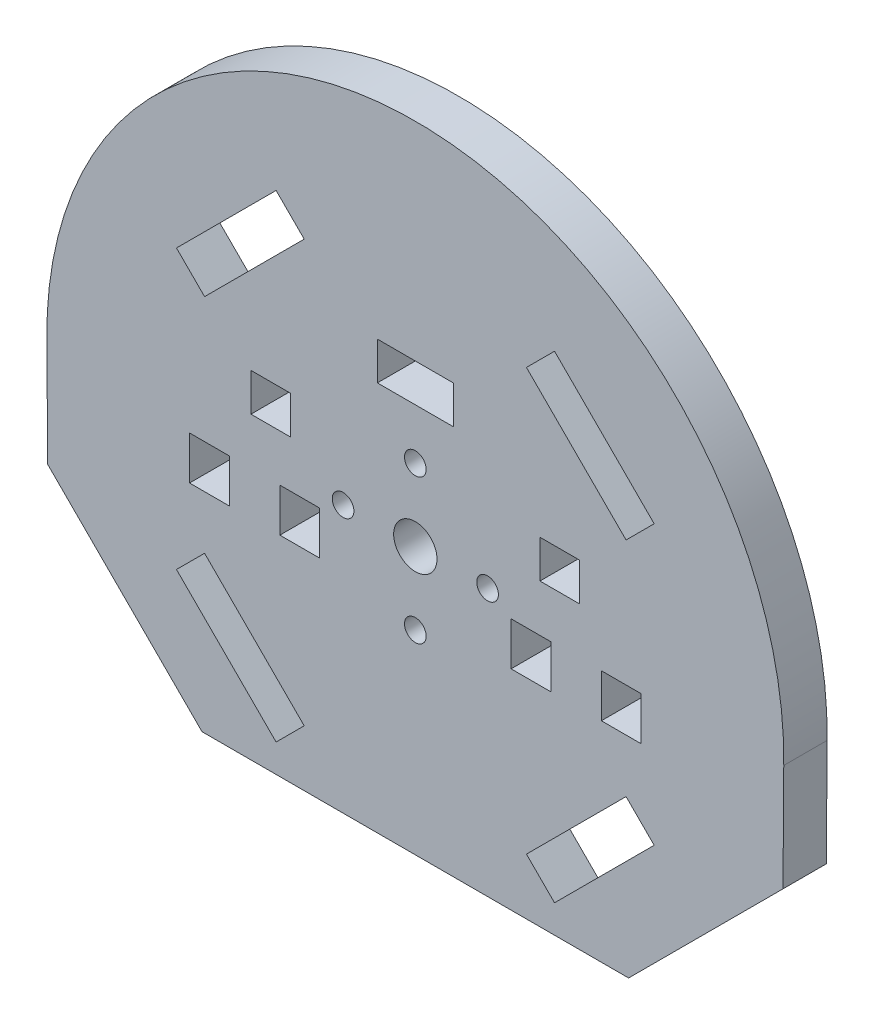
SolidWorks part; units mm, degrees
ref_plane "Front Plane" through (0, 0, 0) normal (0, 0, 1) x (1, 0, 0)
ref_plane "Top Plane" through (0, 0, 0) normal (0, 1, 0) x (1, 0, 0)
ref_plane "Right Plane" through (0, 0, 0) normal (1, 0, 0) x (0, 0, -1)
sketch "Model" plane through (0, 0, 0) normal (0, 0, 1) x (1, 0, 0)
  line L0 (45.297, 69.6215) -> (52.1913, 76.5158)
  line L1 (52.1913, 76.5158) -> (48.3022, 80.4049)
  line L2 (48.3022, 80.4049) -> (34.5136, 66.6163)
  line L3 (34.5136, 66.6163) -> (38.4027, 62.7272)
  line L4 (38.4027, 62.7272) -> (45.297, 69.6215)
  line L5 (45.297, 69.6215) -> (38.4027, 62.7272)
  line L6 (38.4027, 62.7272) -> (34.5136, 66.6163)
  line L7 (34.5136, 66.6163) -> (48.3022, 80.4049)
  line L8 (48.3022, 80.4049) -> (52.1913, 76.5158)
  line L9 (52.1913, 76.5158) -> (45.297, 69.6215)
  line L10 (45.297, 25.0738) -> (52.1913, 18.1795)
  line L11 (52.1913, 18.1795) -> (48.3022, 14.2904)
  line L12 (48.3022, 14.2904) -> (34.5136, 28.079)
  line L13 (34.5136, 28.079) -> (38.4027, 31.9681)
  line L14 (38.4027, 31.9681) -> (45.297, 25.0738)
  line L15 (45.297, 25.0738) -> (38.4027, 31.9681)
  line L16 (38.4027, 31.9681) -> (34.5136, 28.079)
  line L17 (34.5136, 28.079) -> (48.3022, 14.2904)
  line L18 (48.3022, 14.2904) -> (52.1913, 18.1795)
  line L19 (52.1913, 18.1795) -> (45.297, 25.0738)
  line L20 (89.8447, 69.6215) -> (96.739, 62.7272)
  line L21 (96.739, 62.7272) -> (100.6281, 66.6163)
  line L22 (100.6281, 66.6163) -> (86.8395, 80.4049)
  line L23 (86.8395, 80.4049) -> (82.9504, 76.5158)
  line L24 (82.9504, 76.5158) -> (89.8447, 69.6215)
  line L25 (89.8447, 69.6215) -> (82.9504, 76.5158)
  line L26 (82.9504, 76.5158) -> (86.8395, 80.4049)
  line L27 (86.8395, 80.4049) -> (100.6281, 66.6163)
  line L28 (100.6281, 66.6163) -> (96.739, 62.7272)
  line L29 (96.739, 62.7272) -> (89.8447, 69.6215)
  line L30 (89.8447, 25.0738) -> (96.739, 31.9681)
  line L31 (96.739, 31.9681) -> (100.6281, 28.079)
  line L32 (100.6281, 28.079) -> (86.8395, 14.2904)
  line L33 (86.8395, 14.2904) -> (82.9504, 18.1795)
  line L34 (82.9504, 18.1795) -> (89.8447, 25.0738)
  line L35 (89.8447, 25.0738) -> (82.9504, 18.1795)
  line L36 (82.9504, 18.1795) -> (86.8395, 14.2904)
  line L37 (86.8395, 14.2904) -> (100.6281, 28.079)
  line L38 (100.6281, 28.079) -> (96.739, 31.9681)
  line L39 (96.739, 31.9681) -> (89.8447, 25.0738)
  line L40 (34.5136, 28.079) -> (48.3022, 14.2904)
  line L41 (97.0926, 10.4013) -> (38.0491, 10.4013)
  line L42 (67.5708, 10.4013) -> (97.0926, 10.4013)
  line L43 (67.5708, 64.3476) -> (72.8208, 64.3476)
  line L44 (72.8208, 64.3476) -> (72.8208, 69.5976)
  line L45 (72.8208, 69.5976) -> (62.3208, 69.5976)
  line L46 (62.3208, 69.5976) -> (62.3208, 64.3476)
  line L47 (62.3208, 64.3476) -> (67.5708, 64.3476)
  line L48 (97.0926, 10.4013) -> (118.4591, 31.7678)
  line L49 (38.0491, 10.4013) -> (16.6826, 31.7678)
  line L50 (36.3208, 42.3476) -> (36.3208, 45.3476)
  line L51 (36.3208, 45.3476) -> (41.8208, 45.3476)
  line L52 (41.8208, 45.3476) -> (41.8208, 39.3476)
  line L53 (41.8208, 39.3476) -> (36.3208, 39.3476)
  line L54 (36.3208, 39.3476) -> (36.3208, 42.3476)
  line L55 (54.3208, 42.3476) -> (54.3208, 45.3476)
  line L56 (54.3208, 45.3476) -> (48.8208, 45.3476)
  line L57 (48.8208, 39.3476) -> (54.3208, 39.3476)
  line L58 (54.3208, 39.3476) -> (54.3208, 42.3476)
  line L59 (50.3208, 57.0976) -> (50.3208, 51.8476)
  line L60 (50.3208, 51.8476) -> (44.8208, 51.8476)
  line L61 (44.8208, 51.8476) -> (44.8208, 57.0976)
  line L62 (50.3208, 57.0976) -> (44.8208, 57.0976)
  line L63 (98.8208, 42.3476) -> (98.8208, 45.3476)
  line L64 (98.8208, 45.3476) -> (93.3208, 45.3476)
  line L65 (93.3208, 45.3476) -> (93.3208, 39.3476)
  line L66 (93.3208, 39.3476) -> (98.8208, 39.3476)
  line L67 (98.8208, 39.3476) -> (98.8208, 42.3476)
  line L68 (80.8214, 42.3249) -> (80.8214, 45.3249)
  line L69 (80.8214, 45.3249) -> (86.3214, 45.3249)
  line L70 (86.3214, 39.3249) -> (80.8214, 39.3249)
  line L71 (80.8214, 39.3249) -> (80.8214, 42.3249)
  line L72 (84.8208, 57.0976) -> (84.8208, 51.8476)
  line L73 (84.8208, 51.8476) -> (90.3208, 51.8476)
  line L74 (90.3208, 51.8476) -> (90.3208, 57.0976)
  line L75 (84.8208, 57.0976) -> (90.3208, 57.0976)
  line L76 (16.6826, 31.7678) -> (16.5761, 46.6158)
  line L77 (118.4591, 31.7678) -> (118.5656, 46.6158)
  line L78 (48.8208, 39.3476) -> (48.8208, 45.3476)
  line L79 (86.3214, 39.3249) -> (86.3214, 45.3249)
  arc A0 (118.5656, 46.6158) -> (16.5761, 46.6158) centre (67.5708, 47.3476) ccw
  circle A1 centre (67.5708, 47.3476) radius 3
  circle A2 centre (67.5708, 57.3476) radius 1.5
  circle A3 centre (77.5708, 47.3476) radius 1.5
  circle A4 centre (67.5708, 37.3476) radius 1.5
  circle A5 centre (57.5708, 47.3476) radius 1.5
extrude "Boss-Extrude1" add sketch "Model" along normal blind 6 contours A4 | A3 | A5 | A2 | A1 | L12 L13 L14 L10 L11 | L33 L34 L30 L31 L32 | L20 L21 L22 L23 L24 | L4 L0 L1 L2 L3 | L54 L50 L51 L52 L53 | L45 L46 L47 L43 L44 | L48 L77 A0 L76 L49 L41 | L78 L56 L55 L58 L57 | L65 L66 L67 L63 L64 | L59 L60 L61 L62 | L71 L68 L69 L79 L70 | L72 L73 L74 L75
